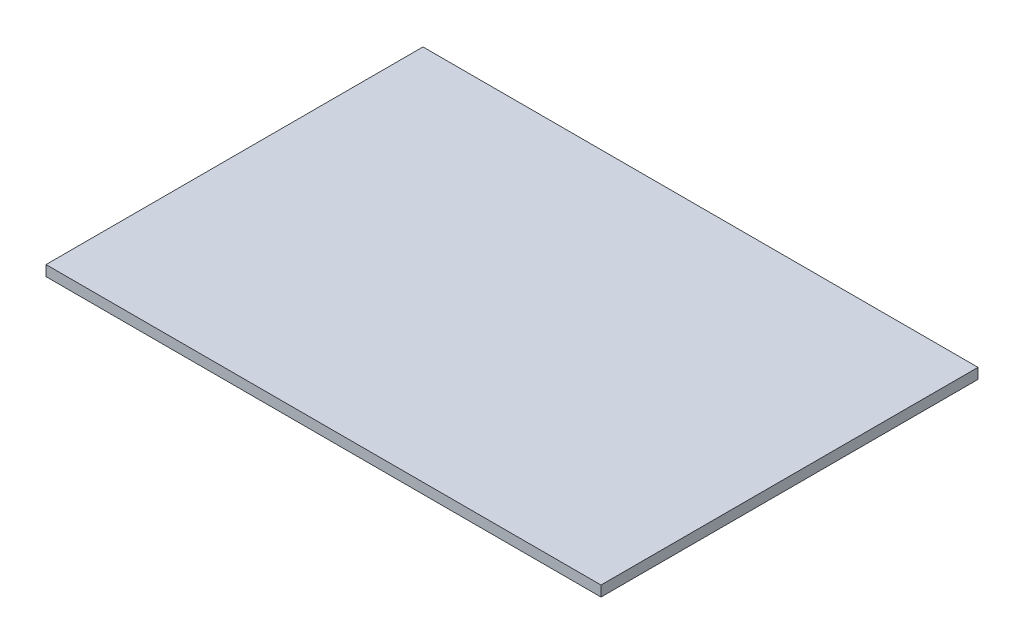
SolidWorks part; units mm, degrees
ref_plane "Спереди" through (0, 0, 0) normal (0, 0, 1) x (1, 0, 0)
ref_plane "Сверху" through (0, 0, 0) normal (0, 1, 0) x (1, 0, 0)
ref_plane "Справа" through (0, 0, 0) normal (1, 0, 0) x (0, 0, -1)
sketch "Эскиз1" plane through (0, 0, 0) normal (0, 1, 0) x (1, 0, 0)
  line L1 (-265, 180) -> (265, 180)
  line L2 (-265, 180) -> (-265, -180)
  line L3 (-265, -180) -> (265, -180)
  line L4 (265, 180) -> (265, -180)
  line L5 (-265, 180) -> (265, -180) construction
  line L6 (-265, -180) -> (265, 180) construction
  point P0 (0, 0)
extrude "Бобышка-Вытянуть1" add sketch "Эскиз1" along normal blind 10
